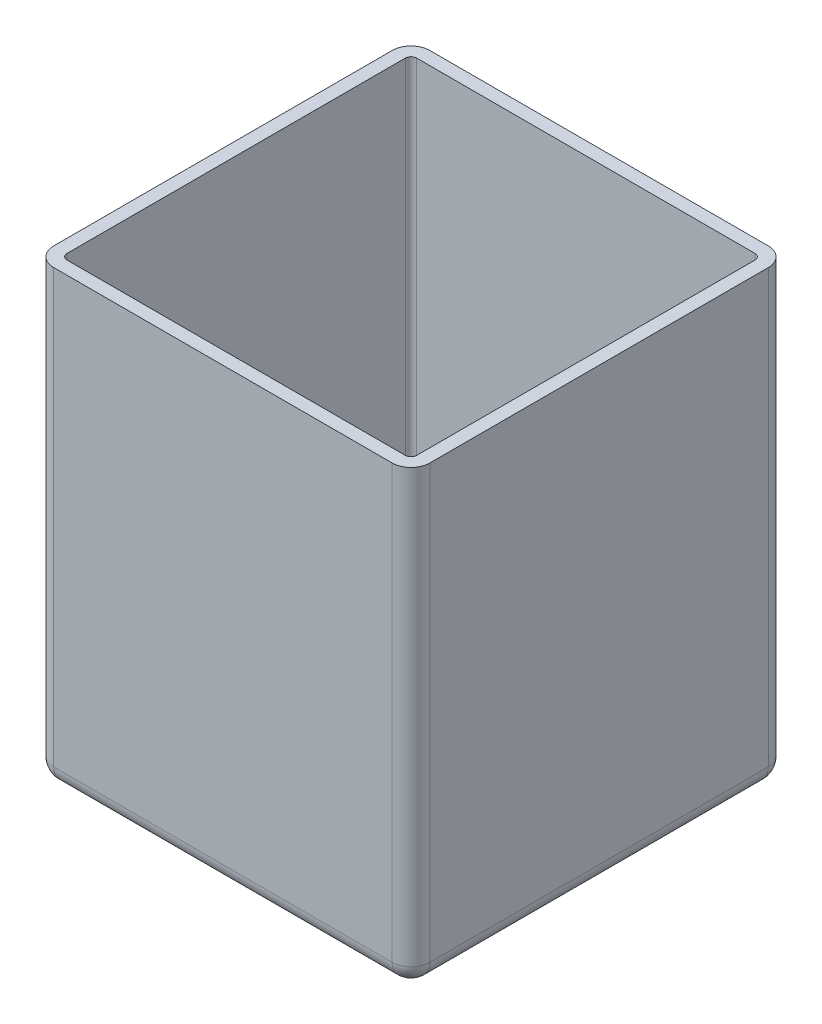
SolidWorks part; units mm, degrees
ref_plane "Front Plane" through (0, 0, 0) normal (0, 0, 1) x (1, 0, 0)
ref_plane "Top Plane" through (0, 0, 0) normal (0, 1, 0) x (1, 0, 0)
ref_plane "Right Plane" through (0, 0, 0) normal (1, 0, 0) x (0, 0, -1)
sketch "Sketch1" plane through (0, 0, 0) normal (0, 1, 0) x (1, 0, 0)
  line L1 (100, 100) -> (-100, 100)
  line L2 (100, 100) -> (100, -100)
  line L3 (100, -100) -> (-100, -100)
  line L4 (-100, 100) -> (-100, -100)
  line L5 (100, 100) -> (-100, -100) construction
  line L6 (100, -100) -> (-100, 100) construction
  point P0 (0, 0)
  dimension "D1" = 200
extrude "Boss-Extrude1" add sketch "Sketch1" along normal blind 240
fillet "Fillet1" radius 10 8 edges at (0, 0, 100) (100, 0, 0) (0, 0, -100) (-100, 0, 0) (-100, 120, 100) (-100, 120, -100) (100, 120, -100) (100, 120, 100)
shell "Shell1" thickness 7
